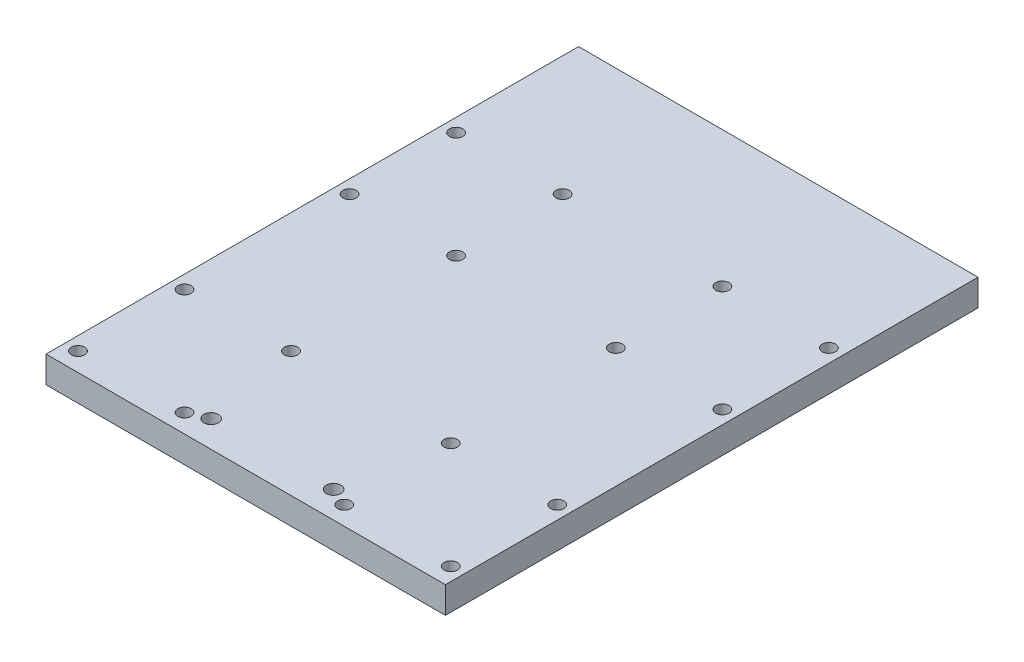
SolidWorks part; units mm, degrees
ref_plane "Front Plane" through (0, 0, 0) normal (0, 0, 1) x (1, 0, 0)
ref_plane "Top Plane" through (0, 0, 0) normal (0, 1, 0) x (1, 0, 0)
ref_plane "Right Plane" through (0, 0, 0) normal (1, 0, 0) x (0, 0, -1)
sketch "Sketch1" plane through (0, 0, 0) normal (0, 1, 0) x (1, 0, 0)
  line L1 (75, -100) -> (-75, -100)
  line L2 (75, -100) -> (75, 100)
  line L3 (75, 100) -> (-75, 100)
  line L4 (-75, -100) -> (-75, 100)
  line L5 (75, -100) -> (-75, 100) construction
  line L6 (75, 100) -> (-75, -100) construction
  point P0 (0, 0)
  dimension "D1" = 150
  dimension "D2" = 200
extrude "Boss-Extrude1" add sketch "Sketch1" along normal blind 10
sketch "Sketch2" plane through (0, 0, 0) normal (0, -1, 0) x (1, 0, 0)
  line L0 (-75, -100) -> (-75, 100) construction
  line L1 (-30, 53) -> (-70, 53) construction
  line L2 (-30, 53) -> (-30, 93) construction
  line L3 (-30, 93) -> (-70, 93) construction
  line L4 (-70, 53) -> (-70, 93) construction
  line L5 (-30, 53) -> (-70, 93) construction
  line L6 (-30, 93) -> (-70, 53) construction
  line L7 (-75, 100) -> (75, 100) construction
  line L8 (0, 100) -> (0, -100) construction
  line L9 (75, -100) -> (-75, -100) construction
  line L10 (30, 93) -> (70, 53) construction
  line L11 (30, 53) -> (70, 93) construction
  line L12 (70, 53) -> (70, 93) construction
  line L13 (30, 93) -> (70, 93) construction
  line L14 (30, 53) -> (30, 93) construction
  line L15 (30, 53) -> (70, 53) construction
  line L16 (-30, -49) -> (-70, -49) construction
  line L17 (-30, -49) -> (-30, -9) construction
  line L18 (-30, -9) -> (-70, -9) construction
  line L19 (-70, -49) -> (-70, -9) construction
  line L20 (-30, -49) -> (-70, -9) construction
  line L21 (-30, -9) -> (-70, -49) construction
  line L22 (30, -9) -> (70, -49) construction
  line L23 (30, -49) -> (70, -9) construction
  line L24 (70, -49) -> (70, -9) construction
  line L25 (30, -9) -> (70, -9) construction
  line L26 (30, -49) -> (30, -9) construction
  line L27 (30, -49) -> (70, -49) construction
  circle A0 centre (-70, 93) radius 2.5
  circle A1 centre (-30, 93) radius 2.5
  circle A2 centre (-30, 53) radius 2.5
  circle A3 centre (-70, 53) radius 2.5
  circle A4 centre (70, 53) radius 2.5
  circle A5 centre (30, 53) radius 2.5
  circle A6 centre (30, 93) radius 2.5
  circle A7 centre (70, 93) radius 2.5
  circle A8 centre (-70, -9) radius 2.5
  circle A9 centre (-30, -9) radius 2.5
  circle A10 centre (-30, -49) radius 2.5
  circle A11 centre (-70, -49) radius 2.5
  circle A12 centre (70, -49) radius 2.5
  circle A13 centre (30, -49) radius 2.5
  circle A14 centre (30, -9) radius 2.5
  circle A15 centre (70, -9) radius 2.5
  circle A16 centre (-23, 90) radius 2.75
  circle A17 centre (23, 90) radius 2.75
  point P0 (-50, 73)
  point P25 (50, 73)
  point P28 (-50, -29)
  point P45 (50, -29)
  dimension "D3" = 5
  dimension "D8" = 5.5
  dimension "D1" = 40
  dimension "D2" = 40
  dimension "D4" = 5
  dimension "D5" = 7
  dimension "D7" = 102
  dimension "D9" = 10
  dimension "D10" = 23
  dimension "D6" = 2
extrude "Cut-Extrude1" cut sketch "Sketch2" against normal through all
